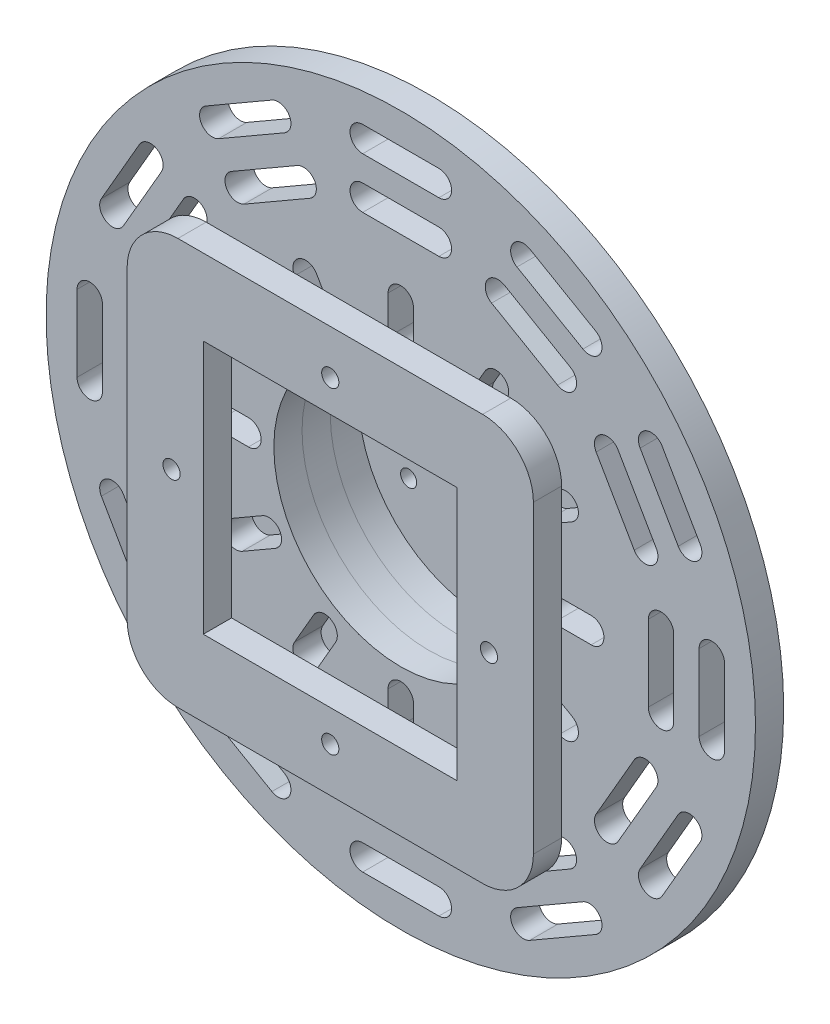
SolidWorks part; units mm, degrees
ref_plane "Front Plane" through (0, 0, 0) normal (0, 0, 1) x (1, 0, 0)
ref_plane "Top Plane" through (0, 0, 0) normal (0, 1, 0) x (1, 0, 0)
ref_plane "Right Plane" through (0, 0, 0) normal (1, 0, 0) x (0, 0, -1)
sketch "Sketch1" plane through (0, 0, 0) normal (0, 0, 1) x (1, 0, 0)
  line L0 (0, -75) -> (0, -60) construction
  line L1 (-5, -75) -> (-5, -60)
  line L2 (5, -75) -> (5, -60)
  line L3 (0, -60) -> (0, 0) construction
  line L4 (-15, -122.5) -> (15, -122.5) construction
  line L7 (-15, -117.5) -> (15, -117.5)
  line L10 (-15, -127.5) -> (15, -127.5)
  line L13 (0, -102.5) -> (0, -122.5) construction
  line L16 (-37.5, -64.9519) -> (-30, -51.9615) construction
  line L19 (-41.8301, -62.4519) -> (-34.3301, -49.4615)
  line L22 (-33.1699, -67.4519) -> (-25.6699, -54.4615)
  line L25 (-64.2404, -81.2676) -> (-38.2596, -96.2676) construction
  line L28 (-61.7404, -76.9375) -> (-35.7596, -91.9375)
  line L31 (-15, -102.5) -> (15, -102.5) construction
  line L32 (-15, -97.5) -> (15, -97.5)
  line L33 (-15, -107.5) -> (15, -107.5)
  line L34 (0, -67.5) -> (0, -102.5) construction
  line L35 (-66.7404, -85.5977) -> (-40.7596, -100.5977)
  line L38 (-74.2404, -98.5881) -> (-48.2596, -113.5881) construction
  line L41 (-71.7404, -94.258) -> (-45.7596, -109.258)
  line L44 (-76.7404, -102.9182) -> (-50.7596, -117.9182)
  line L47 (-64.9519, -37.5) -> (-51.9615, -30) construction
  line L50 (-67.4519, -33.1699) -> (-54.4615, -25.6699)
  line L53 (-62.4519, -41.8301) -> (-49.4615, -34.3301)
  line L56 (-96.2676, -38.2596) -> (-81.2676, -64.2404) construction
  line L59 (-91.9375, -35.7596) -> (-76.9375, -61.7404)
  line L62 (-100.5977, -40.7596) -> (-85.5977, -66.7404)
  line L63 (-113.5881, -48.2596) -> (-98.5881, -74.2404) construction
  line L64 (-109.258, -45.7596) -> (-94.258, -71.7404)
  line L65 (-117.9182, -50.7596) -> (-102.9182, -76.7404)
  line L66 (-75, 0) -> (-60, 0) construction
  line L67 (-75, 5) -> (-60, 5)
  line L68 (-75, -5) -> (-60, -5)
  line L69 (-102.5, 15) -> (-102.5, -15) construction
  line L70 (-97.5, 15) -> (-97.5, -15)
  line L71 (-107.5, 15) -> (-107.5, -15)
  line L72 (-122.5, 15) -> (-122.5, -15) construction
  line L73 (-117.5, 15) -> (-117.5, -15)
  line L74 (-127.5, 15) -> (-127.5, -15)
  line L75 (-64.9519, 37.5) -> (-51.9615, 30) construction
  line L76 (-62.4519, 41.8301) -> (-49.4615, 34.3301)
  line L77 (-67.4519, 33.1699) -> (-54.4615, 25.6699)
  line L78 (-81.2676, 64.2404) -> (-96.2676, 38.2596) construction
  line L79 (-76.9375, 61.7404) -> (-91.9375, 35.7596)
  line L80 (-85.5977, 66.7404) -> (-100.5977, 40.7596)
  line L81 (-98.5881, 74.2404) -> (-113.5881, 48.2596) construction
  line L82 (-94.258, 71.7404) -> (-109.258, 45.7596)
  line L83 (-102.9182, 76.7404) -> (-117.9182, 50.7596)
  line L84 (-37.5, 64.9519) -> (-30, 51.9615) construction
  line L85 (-33.1699, 67.4519) -> (-25.6699, 54.4615)
  line L86 (-41.8301, 62.4519) -> (-34.3301, 49.4615)
  line L87 (-38.2596, 96.2676) -> (-64.2404, 81.2676) construction
  line L88 (-35.7596, 91.9375) -> (-61.7404, 76.9375)
  line L89 (-40.7596, 100.5977) -> (-66.7404, 85.5977)
  line L90 (-48.2596, 113.5881) -> (-74.2404, 98.5881) construction
  line L91 (-45.7596, 109.258) -> (-71.7404, 94.258)
  line L92 (-50.7596, 117.9182) -> (-76.7404, 102.9182)
  line L93 (0, 75) -> (0, 60) construction
  line L94 (5, 75) -> (5, 60)
  line L95 (-5, 75) -> (-5, 60)
  line L96 (15, 102.5) -> (-15, 102.5) construction
  line L97 (15, 97.5) -> (-15, 97.5)
  line L98 (15, 107.5) -> (-15, 107.5)
  line L99 (15, 122.5) -> (-15, 122.5) construction
  line L100 (15, 117.5) -> (-15, 117.5)
  line L101 (15, 127.5) -> (-15, 127.5)
  line L102 (37.5, 64.9519) -> (30, 51.9615) construction
  line L103 (41.8301, 62.4519) -> (34.3301, 49.4615)
  line L104 (33.1699, 67.4519) -> (25.6699, 54.4615)
  line L105 (64.2404, 81.2676) -> (38.2596, 96.2676) construction
  line L106 (61.7404, 76.9375) -> (35.7596, 91.9375)
  line L107 (66.7404, 85.5977) -> (40.7596, 100.5977)
  line L108 (74.2404, 98.5881) -> (48.2596, 113.5881) construction
  line L109 (71.7404, 94.258) -> (45.7596, 109.258)
  line L110 (76.7404, 102.9182) -> (50.7596, 117.9182)
  line L111 (64.9519, 37.5) -> (51.9615, 30) construction
  line L112 (67.4519, 33.1699) -> (54.4615, 25.6699)
  line L113 (62.4519, 41.8301) -> (49.4615, 34.3301)
  line L114 (96.2676, 38.2596) -> (81.2676, 64.2404) construction
  line L115 (91.9375, 35.7596) -> (76.9375, 61.7404)
  line L116 (100.5977, 40.7596) -> (85.5977, 66.7404)
  line L117 (113.5881, 48.2596) -> (98.5881, 74.2404) construction
  line L118 (109.258, 45.7596) -> (94.258, 71.7404)
  line L119 (117.9182, 50.7596) -> (102.9182, 76.7404)
  line L120 (75, 0) -> (60, 0) construction
  line L121 (75, -5) -> (60, -5)
  line L122 (75, 5) -> (60, 5)
  line L123 (102.5, -15) -> (102.5, 15) construction
  line L124 (97.5, -15) -> (97.5, 15)
  line L125 (107.5, -15) -> (107.5, 15)
  line L126 (122.5, -15) -> (122.5, 15) construction
  line L127 (117.5, -15) -> (117.5, 15)
  line L128 (127.5, -15) -> (127.5, 15)
  line L129 (64.9519, -37.5) -> (51.9615, -30) construction
  line L130 (62.4519, -41.8301) -> (49.4615, -34.3301)
  line L131 (67.4519, -33.1699) -> (54.4615, -25.6699)
  line L132 (81.2676, -64.2404) -> (96.2676, -38.2596) construction
  line L133 (76.9375, -61.7404) -> (91.9375, -35.7596)
  line L134 (85.5977, -66.7404) -> (100.5977, -40.7596)
  line L135 (98.5881, -74.2404) -> (113.5881, -48.2596) construction
  line L136 (94.258, -71.7404) -> (109.258, -45.7596)
  line L137 (102.9182, -76.7404) -> (117.9182, -50.7596)
  line L138 (37.5, -64.9519) -> (30, -51.9615) construction
  line L139 (33.1699, -67.4519) -> (25.6699, -54.4615)
  line L140 (41.8301, -62.4519) -> (34.3301, -49.4615)
  line L141 (38.2596, -96.2676) -> (64.2404, -81.2676) construction
  line L142 (35.7596, -91.9375) -> (61.7404, -76.9375)
  line L143 (40.7596, -100.5977) -> (66.7404, -85.5977)
  line L144 (48.2596, -113.5881) -> (74.2404, -98.5881) construction
  line L145 (45.7596, -109.258) -> (71.7404, -94.258)
  line L146 (50.7596, -117.9182) -> (76.7404, -102.9182)
  circle A0 centre (0, 0) radius 139.7
  circle A1 centre (0, 0) radius 25
  arc A2 (-5, -75) -> (5, -75) centre (0, -75) ccw
  arc A3 (5, -60) -> (-5, -60) centre (0, -60) ccw
  arc A22 (-15, -97.5) -> (-15, -107.5) centre (-15, -102.5) ccw
  arc A23 (15, -107.5) -> (15, -97.5) centre (15, -102.5) ccw
  arc A42 (-15, -117.5) -> (-15, -127.5) centre (-15, -122.5) ccw
  arc A43 (15, -127.5) -> (15, -117.5) centre (15, -122.5) ccw
  arc A44 (-41.8301, -62.4519) -> (-33.1699, -67.4519) centre (-37.5, -64.9519) ccw
  arc A45 (-25.6699, -54.4615) -> (-34.3301, -49.4615) centre (-30, -51.9615) ccw
  arc A46 (-61.7404, -76.9375) -> (-66.7404, -85.5977) centre (-64.2404, -81.2676) ccw
  arc A47 (-40.7596, -100.5977) -> (-35.7596, -91.9375) centre (-38.2596, -96.2676) ccw
  arc A48 (-71.7404, -94.258) -> (-76.7404, -102.9182) centre (-74.2404, -98.5881) ccw
  arc A49 (-50.7596, -117.9182) -> (-45.7596, -109.258) centre (-48.2596, -113.5881) ccw
  arc A50 (-67.4519, -33.1699) -> (-62.4519, -41.8301) centre (-64.9519, -37.5) ccw
  arc A51 (-49.4615, -34.3301) -> (-54.4615, -25.6699) centre (-51.9615, -30) ccw
  arc A52 (-91.9375, -35.7596) -> (-100.5977, -40.7596) centre (-96.2676, -38.2596) ccw
  arc A53 (-85.5977, -66.7404) -> (-76.9375, -61.7404) centre (-81.2676, -64.2404) ccw
  arc A54 (-109.258, -45.7596) -> (-117.9182, -50.7596) centre (-113.5881, -48.2596) ccw
  arc A55 (-102.9182, -76.7404) -> (-94.258, -71.7404) centre (-98.5881, -74.2404) ccw
  arc A56 (-75, 5) -> (-75, -5) centre (-75, 0) ccw
  arc A57 (-60, -5) -> (-60, 5) centre (-60, 0) ccw
  arc A58 (-97.5, 15) -> (-107.5, 15) centre (-102.5, 15) ccw
  arc A59 (-107.5, -15) -> (-97.5, -15) centre (-102.5, -15) ccw
  arc A60 (-117.5, 15) -> (-127.5, 15) centre (-122.5, 15) ccw
  arc A61 (-127.5, -15) -> (-117.5, -15) centre (-122.5, -15) ccw
  arc A62 (-62.4519, 41.8301) -> (-67.4519, 33.1699) centre (-64.9519, 37.5) ccw
  arc A63 (-54.4615, 25.6699) -> (-49.4615, 34.3301) centre (-51.9615, 30) ccw
  arc A64 (-76.9375, 61.7404) -> (-85.5977, 66.7404) centre (-81.2676, 64.2404) ccw
  arc A65 (-100.5977, 40.7596) -> (-91.9375, 35.7596) centre (-96.2676, 38.2596) ccw
  arc A66 (-94.258, 71.7404) -> (-102.9182, 76.7404) centre (-98.5881, 74.2404) ccw
  arc A67 (-117.9182, 50.7596) -> (-109.258, 45.7596) centre (-113.5881, 48.2596) ccw
  arc A68 (-33.1699, 67.4519) -> (-41.8301, 62.4519) centre (-37.5, 64.9519) ccw
  arc A69 (-34.3301, 49.4615) -> (-25.6699, 54.4615) centre (-30, 51.9615) ccw
  arc A70 (-35.7596, 91.9375) -> (-40.7596, 100.5977) centre (-38.2596, 96.2676) ccw
  arc A71 (-66.7404, 85.5977) -> (-61.7404, 76.9375) centre (-64.2404, 81.2676) ccw
  arc A72 (-45.7596, 109.258) -> (-50.7596, 117.9182) centre (-48.2596, 113.5881) ccw
  arc A73 (-76.7404, 102.9182) -> (-71.7404, 94.258) centre (-74.2404, 98.5881) ccw
  arc A74 (5, 75) -> (-5, 75) centre (0, 75) ccw
  arc A75 (-5, 60) -> (5, 60) centre (0, 60) ccw
  arc A76 (15, 97.5) -> (15, 107.5) centre (15, 102.5) ccw
  arc A77 (-15, 107.5) -> (-15, 97.5) centre (-15, 102.5) ccw
  arc A78 (15, 117.5) -> (15, 127.5) centre (15, 122.5) ccw
  arc A79 (-15, 127.5) -> (-15, 117.5) centre (-15, 122.5) ccw
  arc A80 (41.8301, 62.4519) -> (33.1699, 67.4519) centre (37.5, 64.9519) ccw
  arc A81 (25.6699, 54.4615) -> (34.3301, 49.4615) centre (30, 51.9615) ccw
  arc A82 (61.7404, 76.9375) -> (66.7404, 85.5977) centre (64.2404, 81.2676) ccw
  arc A83 (40.7596, 100.5977) -> (35.7596, 91.9375) centre (38.2596, 96.2676) ccw
  arc A84 (71.7404, 94.258) -> (76.7404, 102.9182) centre (74.2404, 98.5881) ccw
  arc A85 (50.7596, 117.9182) -> (45.7596, 109.258) centre (48.2596, 113.5881) ccw
  arc A86 (67.4519, 33.1699) -> (62.4519, 41.8301) centre (64.9519, 37.5) ccw
  arc A87 (49.4615, 34.3301) -> (54.4615, 25.6699) centre (51.9615, 30) ccw
  arc A88 (91.9375, 35.7596) -> (100.5977, 40.7596) centre (96.2676, 38.2596) ccw
  arc A89 (85.5977, 66.7404) -> (76.9375, 61.7404) centre (81.2676, 64.2404) ccw
  arc A90 (109.258, 45.7596) -> (117.9182, 50.7596) centre (113.5881, 48.2596) ccw
  arc A91 (102.9182, 76.7404) -> (94.258, 71.7404) centre (98.5881, 74.2404) ccw
  arc A92 (75, -5) -> (75, 5) centre (75, 0) ccw
  arc A93 (60, 5) -> (60, -5) centre (60, 0) ccw
  arc A94 (97.5, -15) -> (107.5, -15) centre (102.5, -15) ccw
  arc A95 (107.5, 15) -> (97.5, 15) centre (102.5, 15) ccw
  arc A96 (117.5, -15) -> (127.5, -15) centre (122.5, -15) ccw
  arc A97 (127.5, 15) -> (117.5, 15) centre (122.5, 15) ccw
  arc A98 (62.4519, -41.8301) -> (67.4519, -33.1699) centre (64.9519, -37.5) ccw
  arc A99 (54.4615, -25.6699) -> (49.4615, -34.3301) centre (51.9615, -30) ccw
  arc A100 (76.9375, -61.7404) -> (85.5977, -66.7404) centre (81.2676, -64.2404) ccw
  arc A101 (100.5977, -40.7596) -> (91.9375, -35.7596) centre (96.2676, -38.2596) ccw
  arc A102 (94.258, -71.7404) -> (102.9182, -76.7404) centre (98.5881, -74.2404) ccw
  arc A103 (117.9182, -50.7596) -> (109.258, -45.7596) centre (113.5881, -48.2596) ccw
  arc A104 (33.1699, -67.4519) -> (41.8301, -62.4519) centre (37.5, -64.9519) ccw
  arc A105 (34.3301, -49.4615) -> (25.6699, -54.4615) centre (30, -51.9615) ccw
  arc A106 (35.7596, -91.9375) -> (40.7596, -100.5977) centre (38.2596, -96.2676) ccw
  arc A107 (66.7404, -85.5977) -> (61.7404, -76.9375) centre (64.2404, -81.2676) ccw
  arc A108 (45.7596, -109.258) -> (50.7596, -117.9182) centre (48.2596, -113.5881) ccw
  arc A109 (76.7404, -102.9182) -> (71.7404, -94.258) centre (74.2404, -98.5881) ccw
  point P6 (0, -67.5)
  point P14 (0, -102.5)
  point P17 (0, -122.5)
  point P29 (-33.75, -58.4567)
  point P36 (-51.25, -88.7676)
  point P39 (-61.25, -106.0881)
  point P51 (-58.4567, -33.75)
  point P60 (-88.7676, -51.25)
  point P63 (-106.0881, -61.25)
  point P75 (-67.5, 0)
  point P78 (-25.429, 35)
  point P89 (-102.5, 0)
  point P93 (-122.5, 0)
  point P105 (-58.4567, 33.75)
  point P113 (-88.7676, 51.25)
  point P116 (-106.0881, 61.25)
  point P127 (-33.75, 58.4567)
  point P135 (-51.25, 88.7676)
  point P138 (-61.25, 106.0881)
  point P151 (0, 67.5)
  point P158 (0, 102.5)
  point P161 (0, 122.5)
  point P172 (33.75, 58.4567)
  point P179 (51.25, 88.7676)
  point P182 (61.25, 106.0881)
  point P193 (58.4567, 33.75)
  point P200 (88.7676, 51.25)
  point P203 (106.0881, 61.25)
  point P214 (67.5, 0)
  point P221 (102.5, 0)
  point P224 (122.5, 0)
  point P235 (58.4567, -33.75)
  point P242 (88.7676, -51.25)
  point P245 (106.0881, -61.25)
  point P256 (33.75, -58.4567)
  point P263 (51.25, -88.7676)
  point P266 (61.25, -106.0881)
  point P275 (0, 0)
  dimension "D1" = 279.4
  dimension "D2" = 50
  dimension "D3" = 60
  dimension "D4" = 15
  dimension "D5" = 10
  dimension "D7" = 30
  dimension "D8" = 10
  dimension "D9" = 35
  dimension "D6" = 20
  dimension "D10" = 12
sketch "Sketch4" plane through (0, 0, 0) normal (0, 0, 1) x (1, 0, 0)
  circle A0 centre (0, 0) radius 12.7
  circle A1 centre (0, 0) radius 75
  circle A2 centre (30.2459, 17.4625) radius 3.175 construction
  circle A3 centre (-30.2459, 17.4625) radius 3.175 construction
  circle A4 centre (0, -34.925) radius 3.175 construction
  circle A5 centre (30.2459, 17.4625) radius 3.175
  circle A6 centre (-30.2459, 17.4625) radius 3.175
  circle A7 centre (0, -34.925) radius 3.175
  arc A8 (-2.2451, 37.1701) -> (0.3966, 38.0751) centre (0, 34.925) ccw construction
  arc A9 (0.3966, 38.0751) -> (-2.2451, 37.1701) centre (0, 34.925) ccw construction
  arc A10 (-2.2451, 37.1701) -> (0.3966, 38.0751) centre (0, 34.925) ccw
  arc A11 (0.3966, 38.0751) -> (-2.2451, 37.1701) centre (0, 34.925) ccw
  arc A12 (-31.0677, -20.5293) -> (-33.1723, -18.6941) centre (-30.2459, -17.4625) ccw construction
  arc A13 (-33.1723, -18.6941) -> (-31.0677, -20.5293) centre (-30.2459, -17.4625) ccw construction
  arc A14 (-31.0677, -20.5293) -> (-33.1723, -18.6941) centre (-30.2459, -17.4625) ccw
  arc A15 (-33.1723, -18.6941) -> (-31.0677, -20.5293) centre (-30.2459, -17.4625) ccw
  arc A16 (33.3128, -16.6407) -> (32.7757, -19.381) centre (30.2459, -17.4625) ccw construction
  arc A17 (32.7757, -19.381) -> (33.3128, -16.6407) centre (30.2459, -17.4625) ccw construction
  arc A18 (33.3128, -16.6407) -> (32.7757, -19.381) centre (30.2459, -17.4625) ccw
  arc A19 (32.7757, -19.381) -> (33.3128, -16.6407) centre (30.2459, -17.4625) ccw
  dimension "D1" = 150
  dimension "D2" = 25.4
extrude "Boss-Extrude1" add sketch "Sketch4" along normal blind 11.1125
sketch "Sketch5" plane through (0, 0, 11.1125) normal (0, 0, 1) x (1, 0, 0)
  circle A0 centre (0, 0) radius 50
  circle A1 centre (0, 0) radius 75
  dimension "D1" = 100
  dimension "D2" = 150
extrude "Boss-Extrude2" add sketch "Sketch5" along normal blind 11.1125 separate body
sketch "Sketch6" plane through (0, 0, 22.225) normal (0, 0, 1) x (1, 0, 0)
  circle A0 centre (0, 0) radius 50
  circle A1 centre (0, 0) radius 90
  dimension "D1" = 180
  dimension "D2" = 100
extrude "Boss-Extrude3" add sketch "Sketch6" along normal blind 11.1125
sketch "Sketch7" plane through (0, 0, 33.3375) normal (0, 0, 1) x (1, 0, 0)
  line L2 (-5, -60) -> (-5, -75)
  line L3 (5, -75) -> (5, -60)
  line L4 (-5, -60) -> (-5, -75)
  line L5 (5, -75) -> (5, -60)
  line L6 (15, -117.5) -> (-15, -117.5)
  line L7 (-15, -127.5) -> (15, -127.5)
  line L8 (15, -117.5) -> (-15, -117.5)
  line L9 (-15, -127.5) -> (15, -127.5)
  line L10 (-45.7596, -109.258) -> (-71.7404, -94.258)
  line L11 (-76.7404, -102.9182) -> (-50.7596, -117.9182)
  line L12 (-45.7596, -109.258) -> (-71.7404, -94.258)
  line L13 (-76.7404, -102.9182) -> (-50.7596, -117.9182)
  line L14 (-33.1699, -67.4519) -> (-25.6699, -54.4615)
  line L15 (-34.3301, -49.4615) -> (-41.8301, -62.4519)
  line L16 (-33.1699, -67.4519) -> (-25.6699, -54.4615)
  line L17 (-34.3301, -49.4615) -> (-41.8301, -62.4519)
  line L18 (-54.4615, -25.6699) -> (-67.4519, -33.1699)
  line L19 (-62.4519, -41.8301) -> (-49.4615, -34.3301)
  line L20 (-54.4615, -25.6699) -> (-67.4519, -33.1699)
  line L21 (-62.4519, -41.8301) -> (-49.4615, -34.3301)
  line L22 (-35.7596, -91.9375) -> (-61.7404, -76.9375)
  line L23 (-66.7404, -85.5977) -> (-40.7596, -100.5977)
  line L24 (-35.7596, -91.9375) -> (-61.7404, -76.9375)
  line L25 (-66.7404, -85.5977) -> (-40.7596, -100.5977)
  line L26 (-94.258, -71.7404) -> (-109.258, -45.7596)
  line L27 (-117.9182, -50.7596) -> (-102.9182, -76.7404)
  line L28 (-94.258, -71.7404) -> (-109.258, -45.7596)
  line L29 (-117.9182, -50.7596) -> (-102.9182, -76.7404)
  line L30 (-76.9375, -61.7404) -> (-91.9375, -35.7596)
  line L31 (-100.5977, -40.7596) -> (-85.5977, -66.7404)
  line L32 (-76.9375, -61.7404) -> (-91.9375, -35.7596)
  line L33 (-100.5977, -40.7596) -> (-85.5977, -66.7404)
  line L34 (-75, -5) -> (-60, -5)
  line L35 (-60, 5) -> (-75, 5)
  line L36 (-75, -5) -> (-60, -5)
  line L37 (-60, 5) -> (-75, 5)
  line L38 (-15, -107.5) -> (15, -107.5)
  line L39 (15, -97.5) -> (-15, -97.5)
  line L40 (-15, -107.5) -> (15, -107.5)
  line L41 (15, -97.5) -> (-15, -97.5)
  line L42 (-49.4615, 34.3301) -> (-62.4519, 41.8301)
  line L43 (-67.4519, 33.1699) -> (-54.4615, 25.6699)
  line L44 (-49.4615, 34.3301) -> (-62.4519, 41.8301)
  line L45 (-67.4519, 33.1699) -> (-54.4615, 25.6699)
  line L46 (-127.5, 15) -> (-127.5, -15)
  line L47 (-117.5, -15) -> (-117.5, 15)
  line L48 (-127.5, 15) -> (-127.5, -15)
  line L49 (-117.5, -15) -> (-117.5, 15)
  line L50 (-97.5, -15) -> (-97.5, 15)
  line L51 (-107.5, 15) -> (-107.5, -15)
  line L52 (-97.5, -15) -> (-97.5, 15)
  line L53 (-107.5, 15) -> (-107.5, -15)
  line L54 (-109.258, 45.7596) -> (-94.258, 71.7404)
  line L55 (-102.9182, 76.7404) -> (-117.9182, 50.7596)
  line L56 (-109.258, 45.7596) -> (-94.258, 71.7404)
  line L57 (-102.9182, 76.7404) -> (-117.9182, 50.7596)
  line L58 (-91.9375, 35.7596) -> (-76.9375, 61.7404)
  line L59 (-85.5977, 66.7404) -> (-100.5977, 40.7596)
  line L60 (-91.9375, 35.7596) -> (-76.9375, 61.7404)
  line L61 (-85.5977, 66.7404) -> (-100.5977, 40.7596)
  line L62 (-71.7404, 94.258) -> (-45.7596, 109.258)
  line L63 (-50.7596, 117.9182) -> (-76.7404, 102.9182)
  line L64 (-71.7404, 94.258) -> (-45.7596, 109.258)
  line L65 (-50.7596, 117.9182) -> (-76.7404, 102.9182)
  line L66 (-25.6699, 54.4615) -> (-33.1699, 67.4519)
  line L67 (-41.8301, 62.4519) -> (-34.3301, 49.4615)
  line L68 (-25.6699, 54.4615) -> (-33.1699, 67.4519)
  line L69 (-41.8301, 62.4519) -> (-34.3301, 49.4615)
  line L70 (5, 60) -> (5, 75)
  line L71 (-5, 75) -> (-5, 60)
  line L72 (5, 60) -> (5, 75)
  line L73 (-5, 75) -> (-5, 60)
  line L74 (-61.7404, 76.9375) -> (-35.7596, 91.9375)
  line L75 (-40.7596, 100.5977) -> (-66.7404, 85.5977)
  line L76 (-61.7404, 76.9375) -> (-35.7596, 91.9375)
  line L77 (-40.7596, 100.5977) -> (-66.7404, 85.5977)
  line L78 (-15, 117.5) -> (15, 117.5)
  line L79 (15, 127.5) -> (-15, 127.5)
  line L80 (-15, 117.5) -> (15, 117.5)
  line L81 (15, 127.5) -> (-15, 127.5)
  line L82 (-15, 97.5) -> (15, 97.5)
  line L83 (15, 107.5) -> (-15, 107.5)
  line L84 (-15, 97.5) -> (15, 97.5)
  line L85 (15, 107.5) -> (-15, 107.5)
  line L86 (45.7596, 109.258) -> (71.7404, 94.258)
  line L87 (76.7404, 102.9182) -> (50.7596, 117.9182)
  line L88 (45.7596, 109.258) -> (71.7404, 94.258)
  line L89 (76.7404, 102.9182) -> (50.7596, 117.9182)
  line L90 (35.7596, 91.9375) -> (61.7404, 76.9375)
  line L91 (66.7404, 85.5977) -> (40.7596, 100.5977)
  line L92 (35.7596, 91.9375) -> (61.7404, 76.9375)
  line L93 (66.7404, 85.5977) -> (40.7596, 100.5977)
  line L94 (34.3301, 49.4615) -> (41.8301, 62.4519)
  line L95 (33.1699, 67.4519) -> (25.6699, 54.4615)
  line L96 (34.3301, 49.4615) -> (41.8301, 62.4519)
  line L97 (33.1699, 67.4519) -> (25.6699, 54.4615)
  line L98 (94.258, 71.7404) -> (109.258, 45.7596)
  line L99 (117.9182, 50.7596) -> (102.9182, 76.7404)
  line L100 (94.258, 71.7404) -> (109.258, 45.7596)
  line L101 (117.9182, 50.7596) -> (102.9182, 76.7404)
  line L102 (54.4615, 25.6699) -> (67.4519, 33.1699)
  line L103 (62.4519, 41.8301) -> (49.4615, 34.3301)
  line L104 (54.4615, 25.6699) -> (67.4519, 33.1699)
  line L105 (62.4519, 41.8301) -> (49.4615, 34.3301)
  line L106 (60, -5) -> (75, -5)
  line L107 (75, 5) -> (60, 5)
  line L108 (60, -5) -> (75, -5)
  line L109 (75, 5) -> (60, 5)
  line L110 (76.9375, 61.7404) -> (91.9375, 35.7596)
  line L111 (100.5977, 40.7596) -> (85.5977, 66.7404)
  line L112 (76.9375, 61.7404) -> (91.9375, 35.7596)
  line L113 (100.5977, 40.7596) -> (85.5977, 66.7404)
  line L114 (49.4615, -34.3301) -> (62.4519, -41.8301)
  line L115 (67.4519, -33.1699) -> (54.4615, -25.6699)
  line L116 (49.4615, -34.3301) -> (62.4519, -41.8301)
  line L117 (67.4519, -33.1699) -> (54.4615, -25.6699)
  line L118 (117.5, 15) -> (117.5, -15)
  line L119 (127.5, -15) -> (127.5, 15)
  line L120 (117.5, 15) -> (117.5, -15)
  line L121 (127.5, -15) -> (127.5, 15)
  line L122 (97.5, 15) -> (97.5, -15)
  line L123 (107.5, -15) -> (107.5, 15)
  line L124 (97.5, 15) -> (97.5, -15)
  line L125 (107.5, -15) -> (107.5, 15)
  line L126 (109.258, -45.7596) -> (94.258, -71.7404)
  line L127 (102.9182, -76.7404) -> (117.9182, -50.7596)
  line L128 (109.258, -45.7596) -> (94.258, -71.7404)
  line L129 (102.9182, -76.7404) -> (117.9182, -50.7596)
  line L130 (91.9375, -35.7596) -> (76.9375, -61.7404)
  line L131 (85.5977, -66.7404) -> (100.5977, -40.7596)
  line L132 (91.9375, -35.7596) -> (76.9375, -61.7404)
  line L133 (85.5977, -66.7404) -> (100.5977, -40.7596)
  line L134 (71.7404, -94.258) -> (45.7596, -109.258)
  line L135 (50.7596, -117.9182) -> (76.7404, -102.9182)
  line L136 (71.7404, -94.258) -> (45.7596, -109.258)
  line L137 (50.7596, -117.9182) -> (76.7404, -102.9182)
  line L138 (61.7404, -76.9375) -> (35.7596, -91.9375)
  line L139 (40.7596, -100.5977) -> (66.7404, -85.5977)
  line L140 (61.7404, -76.9375) -> (35.7596, -91.9375)
  line L141 (40.7596, -100.5977) -> (66.7404, -85.5977)
  line L142 (25.6699, -54.4615) -> (33.1699, -67.4519)
  line L143 (41.8301, -62.4519) -> (34.3301, -49.4615)
  line L144 (25.6699, -54.4615) -> (33.1699, -67.4519)
  line L145 (41.8301, -62.4519) -> (34.3301, -49.4615)
  circle A0 centre (0, 0) radius 50
  circle A3 centre (0, 0) radius 139.7
  circle A4 centre (0, 0) radius 139.7
  arc A6 (5, -60) -> (-5, -60) centre (0, -60) ccw
  arc A7 (-5, -75) -> (5, -75) centre (0, -75) ccw
  arc A8 (5, -60) -> (-5, -60) centre (0, -60) ccw
  arc A9 (-5, -75) -> (5, -75) centre (0, -75) ccw
  arc A10 (15, -127.5) -> (15, -117.5) centre (15, -122.5) ccw
  arc A11 (-15, -117.5) -> (-15, -127.5) centre (-15, -122.5) ccw
  arc A12 (15, -127.5) -> (15, -117.5) centre (15, -122.5) ccw
  arc A13 (-15, -117.5) -> (-15, -127.5) centre (-15, -122.5) ccw
  arc A14 (-50.7596, -117.9182) -> (-45.7596, -109.258) centre (-48.2596, -113.5881) ccw
  arc A15 (-71.7404, -94.258) -> (-76.7404, -102.9182) centre (-74.2404, -98.5881) ccw
  arc A16 (-50.7596, -117.9182) -> (-45.7596, -109.258) centre (-48.2596, -113.5881) ccw
  arc A17 (-71.7404, -94.258) -> (-76.7404, -102.9182) centre (-74.2404, -98.5881) ccw
  arc A18 (-25.6699, -54.4615) -> (-34.3301, -49.4615) centre (-30, -51.9615) ccw
  arc A19 (-41.8301, -62.4519) -> (-33.1699, -67.4519) centre (-37.5, -64.9519) ccw
  arc A20 (-25.6699, -54.4615) -> (-34.3301, -49.4615) centre (-30, -51.9615) ccw
  arc A21 (-41.8301, -62.4519) -> (-33.1699, -67.4519) centre (-37.5, -64.9519) ccw
  arc A22 (-49.4615, -34.3301) -> (-54.4615, -25.6699) centre (-51.9615, -30) ccw
  arc A23 (-67.4519, -33.1699) -> (-62.4519, -41.8301) centre (-64.9519, -37.5) ccw
  arc A24 (-49.4615, -34.3301) -> (-54.4615, -25.6699) centre (-51.9615, -30) ccw
  arc A25 (-67.4519, -33.1699) -> (-62.4519, -41.8301) centre (-64.9519, -37.5) ccw
  arc A26 (-40.7596, -100.5977) -> (-35.7596, -91.9375) centre (-38.2596, -96.2676) ccw
  arc A27 (-61.7404, -76.9375) -> (-66.7404, -85.5977) centre (-64.2404, -81.2676) ccw
  arc A28 (-40.7596, -100.5977) -> (-35.7596, -91.9375) centre (-38.2596, -96.2676) ccw
  arc A29 (-61.7404, -76.9375) -> (-66.7404, -85.5977) centre (-64.2404, -81.2676) ccw
  arc A30 (-102.9182, -76.7404) -> (-94.258, -71.7404) centre (-98.5881, -74.2404) ccw
  arc A31 (-109.258, -45.7596) -> (-117.9182, -50.7596) centre (-113.5881, -48.2596) ccw
  arc A32 (-102.9182, -76.7404) -> (-94.258, -71.7404) centre (-98.5881, -74.2404) ccw
  arc A33 (-109.258, -45.7596) -> (-117.9182, -50.7596) centre (-113.5881, -48.2596) ccw
  arc A34 (-85.5977, -66.7404) -> (-76.9375, -61.7404) centre (-81.2676, -64.2404) ccw
  arc A35 (-91.9375, -35.7596) -> (-100.5977, -40.7596) centre (-96.2676, -38.2596) ccw
  arc A36 (-85.5977, -66.7404) -> (-76.9375, -61.7404) centre (-81.2676, -64.2404) ccw
  arc A37 (-91.9375, -35.7596) -> (-100.5977, -40.7596) centre (-96.2676, -38.2596) ccw
  arc A38 (-60, -5) -> (-60, 5) centre (-60, 0) ccw
  arc A39 (-75, 5) -> (-75, -5) centre (-75, 0) ccw
  arc A40 (-60, -5) -> (-60, 5) centre (-60, 0) ccw
  arc A41 (-75, 5) -> (-75, -5) centre (-75, 0) ccw
  arc A42 (15, -107.5) -> (15, -97.5) centre (15, -102.5) ccw
  arc A43 (-15, -97.5) -> (-15, -107.5) centre (-15, -102.5) ccw
  arc A44 (15, -107.5) -> (15, -97.5) centre (15, -102.5) ccw
  arc A45 (-15, -97.5) -> (-15, -107.5) centre (-15, -102.5) ccw
  arc A46 (-54.4615, 25.6699) -> (-49.4615, 34.3301) centre (-51.9615, 30) ccw
  arc A47 (-62.4519, 41.8301) -> (-67.4519, 33.1699) centre (-64.9519, 37.5) ccw
  arc A48 (-54.4615, 25.6699) -> (-49.4615, 34.3301) centre (-51.9615, 30) ccw
  arc A49 (-62.4519, 41.8301) -> (-67.4519, 33.1699) centre (-64.9519, 37.5) ccw
  arc A50 (-127.5, -15) -> (-117.5, -15) centre (-122.5, -15) ccw
  arc A51 (-117.5, 15) -> (-127.5, 15) centre (-122.5, 15) ccw
  arc A52 (-127.5, -15) -> (-117.5, -15) centre (-122.5, -15) ccw
  arc A53 (-117.5, 15) -> (-127.5, 15) centre (-122.5, 15) ccw
  arc A54 (-107.5, -15) -> (-97.5, -15) centre (-102.5, -15) ccw
  arc A55 (-97.5, 15) -> (-107.5, 15) centre (-102.5, 15) ccw
  arc A56 (-107.5, -15) -> (-97.5, -15) centre (-102.5, -15) ccw
  arc A57 (-97.5, 15) -> (-107.5, 15) centre (-102.5, 15) ccw
  arc A58 (-117.9182, 50.7596) -> (-109.258, 45.7596) centre (-113.5881, 48.2596) ccw
  arc A59 (-94.258, 71.7404) -> (-102.9182, 76.7404) centre (-98.5881, 74.2404) ccw
  arc A60 (-117.9182, 50.7596) -> (-109.258, 45.7596) centre (-113.5881, 48.2596) ccw
  arc A61 (-94.258, 71.7404) -> (-102.9182, 76.7404) centre (-98.5881, 74.2404) ccw
  arc A62 (-100.5977, 40.7596) -> (-91.9375, 35.7596) centre (-96.2676, 38.2596) ccw
  arc A63 (-76.9375, 61.7404) -> (-85.5977, 66.7404) centre (-81.2676, 64.2404) ccw
  arc A64 (-100.5977, 40.7596) -> (-91.9375, 35.7596) centre (-96.2676, 38.2596) ccw
  arc A65 (-76.9375, 61.7404) -> (-85.5977, 66.7404) centre (-81.2676, 64.2404) ccw
  arc A66 (-76.7404, 102.9182) -> (-71.7404, 94.258) centre (-74.2404, 98.5881) ccw
  arc A67 (-45.7596, 109.258) -> (-50.7596, 117.9182) centre (-48.2596, 113.5881) ccw
  arc A68 (-76.7404, 102.9182) -> (-71.7404, 94.258) centre (-74.2404, 98.5881) ccw
  arc A69 (-45.7596, 109.258) -> (-50.7596, 117.9182) centre (-48.2596, 113.5881) ccw
  arc A70 (-34.3301, 49.4615) -> (-25.6699, 54.4615) centre (-30, 51.9615) ccw
  arc A71 (-33.1699, 67.4519) -> (-41.8301, 62.4519) centre (-37.5, 64.9519) ccw
  arc A72 (-34.3301, 49.4615) -> (-25.6699, 54.4615) centre (-30, 51.9615) ccw
  arc A73 (-33.1699, 67.4519) -> (-41.8301, 62.4519) centre (-37.5, 64.9519) ccw
  arc A74 (-5, 60) -> (5, 60) centre (0, 60) ccw
  arc A75 (5, 75) -> (-5, 75) centre (0, 75) ccw
  arc A76 (-5, 60) -> (5, 60) centre (0, 60) ccw
  arc A77 (5, 75) -> (-5, 75) centre (0, 75) ccw
  arc A78 (-66.7404, 85.5977) -> (-61.7404, 76.9375) centre (-64.2404, 81.2676) ccw
  arc A79 (-35.7596, 91.9375) -> (-40.7596, 100.5977) centre (-38.2596, 96.2676) ccw
  arc A80 (-66.7404, 85.5977) -> (-61.7404, 76.9375) centre (-64.2404, 81.2676) ccw
  arc A81 (-35.7596, 91.9375) -> (-40.7596, 100.5977) centre (-38.2596, 96.2676) ccw
  arc A82 (-15, 127.5) -> (-15, 117.5) centre (-15, 122.5) ccw
  arc A83 (15, 117.5) -> (15, 127.5) centre (15, 122.5) ccw
  arc A84 (-15, 127.5) -> (-15, 117.5) centre (-15, 122.5) ccw
  arc A85 (15, 117.5) -> (15, 127.5) centre (15, 122.5) ccw
  arc A86 (-15, 107.5) -> (-15, 97.5) centre (-15, 102.5) ccw
  arc A87 (15, 97.5) -> (15, 107.5) centre (15, 102.5) ccw
  arc A88 (-15, 107.5) -> (-15, 97.5) centre (-15, 102.5) ccw
  arc A89 (15, 97.5) -> (15, 107.5) centre (15, 102.5) ccw
  arc A90 (50.7596, 117.9182) -> (45.7596, 109.258) centre (48.2596, 113.5881) ccw
  arc A91 (71.7404, 94.258) -> (76.7404, 102.9182) centre (74.2404, 98.5881) ccw
  arc A92 (50.7596, 117.9182) -> (45.7596, 109.258) centre (48.2596, 113.5881) ccw
  arc A93 (71.7404, 94.258) -> (76.7404, 102.9182) centre (74.2404, 98.5881) ccw
  arc A94 (40.7596, 100.5977) -> (35.7596, 91.9375) centre (38.2596, 96.2676) ccw
  arc A95 (61.7404, 76.9375) -> (66.7404, 85.5977) centre (64.2404, 81.2676) ccw
  arc A96 (40.7596, 100.5977) -> (35.7596, 91.9375) centre (38.2596, 96.2676) ccw
  arc A97 (61.7404, 76.9375) -> (66.7404, 85.5977) centre (64.2404, 81.2676) ccw
  arc A98 (25.6699, 54.4615) -> (34.3301, 49.4615) centre (30, 51.9615) ccw
  arc A99 (41.8301, 62.4519) -> (33.1699, 67.4519) centre (37.5, 64.9519) ccw
  arc A100 (25.6699, 54.4615) -> (34.3301, 49.4615) centre (30, 51.9615) ccw
  arc A101 (41.8301, 62.4519) -> (33.1699, 67.4519) centre (37.5, 64.9519) ccw
  arc A102 (102.9182, 76.7404) -> (94.258, 71.7404) centre (98.5881, 74.2404) ccw
  arc A103 (109.258, 45.7596) -> (117.9182, 50.7596) centre (113.5881, 48.2596) ccw
  arc A104 (102.9182, 76.7404) -> (94.258, 71.7404) centre (98.5881, 74.2404) ccw
  arc A105 (109.258, 45.7596) -> (117.9182, 50.7596) centre (113.5881, 48.2596) ccw
  arc A106 (49.4615, 34.3301) -> (54.4615, 25.6699) centre (51.9615, 30) ccw
  arc A107 (67.4519, 33.1699) -> (62.4519, 41.8301) centre (64.9519, 37.5) ccw
  arc A108 (49.4615, 34.3301) -> (54.4615, 25.6699) centre (51.9615, 30) ccw
  arc A109 (67.4519, 33.1699) -> (62.4519, 41.8301) centre (64.9519, 37.5) ccw
  arc A110 (60, 5) -> (60, -5) centre (60, 0) ccw
  arc A111 (75, -5) -> (75, 5) centre (75, 0) ccw
  arc A112 (60, 5) -> (60, -5) centre (60, 0) ccw
  arc A113 (75, -5) -> (75, 5) centre (75, 0) ccw
  arc A114 (85.5977, 66.7404) -> (76.9375, 61.7404) centre (81.2676, 64.2404) ccw
  arc A115 (91.9375, 35.7596) -> (100.5977, 40.7596) centre (96.2676, 38.2596) ccw
  arc A116 (85.5977, 66.7404) -> (76.9375, 61.7404) centre (81.2676, 64.2404) ccw
  arc A117 (91.9375, 35.7596) -> (100.5977, 40.7596) centre (96.2676, 38.2596) ccw
  arc A118 (54.4615, -25.6699) -> (49.4615, -34.3301) centre (51.9615, -30) ccw
  arc A119 (62.4519, -41.8301) -> (67.4519, -33.1699) centre (64.9519, -37.5) ccw
  arc A120 (54.4615, -25.6699) -> (49.4615, -34.3301) centre (51.9615, -30) ccw
  arc A121 (62.4519, -41.8301) -> (67.4519, -33.1699) centre (64.9519, -37.5) ccw
  arc A122 (127.5, 15) -> (117.5, 15) centre (122.5, 15) ccw
  arc A123 (117.5, -15) -> (127.5, -15) centre (122.5, -15) ccw
  arc A124 (127.5, 15) -> (117.5, 15) centre (122.5, 15) ccw
  arc A125 (117.5, -15) -> (127.5, -15) centre (122.5, -15) ccw
  arc A126 (107.5, 15) -> (97.5, 15) centre (102.5, 15) ccw
  arc A127 (97.5, -15) -> (107.5, -15) centre (102.5, -15) ccw
  arc A128 (107.5, 15) -> (97.5, 15) centre (102.5, 15) ccw
  arc A129 (97.5, -15) -> (107.5, -15) centre (102.5, -15) ccw
  arc A130 (117.9182, -50.7596) -> (109.258, -45.7596) centre (113.5881, -48.2596) ccw
  arc A131 (94.258, -71.7404) -> (102.9182, -76.7404) centre (98.5881, -74.2404) ccw
  arc A132 (117.9182, -50.7596) -> (109.258, -45.7596) centre (113.5881, -48.2596) ccw
  arc A133 (94.258, -71.7404) -> (102.9182, -76.7404) centre (98.5881, -74.2404) ccw
  arc A134 (100.5977, -40.7596) -> (91.9375, -35.7596) centre (96.2676, -38.2596) ccw
  arc A135 (76.9375, -61.7404) -> (85.5977, -66.7404) centre (81.2676, -64.2404) ccw
  arc A136 (100.5977, -40.7596) -> (91.9375, -35.7596) centre (96.2676, -38.2596) ccw
  arc A137 (76.9375, -61.7404) -> (85.5977, -66.7404) centre (81.2676, -64.2404) ccw
  arc A138 (76.7404, -102.9182) -> (71.7404, -94.258) centre (74.2404, -98.5881) ccw
  arc A139 (45.7596, -109.258) -> (50.7596, -117.9182) centre (48.2596, -113.5881) ccw
  arc A140 (76.7404, -102.9182) -> (71.7404, -94.258) centre (74.2404, -98.5881) ccw
  arc A141 (45.7596, -109.258) -> (50.7596, -117.9182) centre (48.2596, -113.5881) ccw
  arc A142 (66.7404, -85.5977) -> (61.7404, -76.9375) centre (64.2404, -81.2676) ccw
  arc A143 (35.7596, -91.9375) -> (40.7596, -100.5977) centre (38.2596, -96.2676) ccw
  arc A144 (66.7404, -85.5977) -> (61.7404, -76.9375) centre (64.2404, -81.2676) ccw
  arc A145 (35.7596, -91.9375) -> (40.7596, -100.5977) centre (38.2596, -96.2676) ccw
  arc A146 (34.3301, -49.4615) -> (25.6699, -54.4615) centre (30, -51.9615) ccw
  arc A147 (33.1699, -67.4519) -> (41.8301, -62.4519) centre (37.5, -64.9519) ccw
  arc A148 (34.3301, -49.4615) -> (25.6699, -54.4615) centre (30, -51.9615) ccw
  arc A149 (33.1699, -67.4519) -> (41.8301, -62.4519) centre (37.5, -64.9519) ccw
  circle M147 centre (0, 0) radius 90
  dimension "D2" = 0
  dimension "D3" = 0
  dimension "D4" = 0
  dimension "D5" = 0
  dimension "D6" = 0
  dimension "D7" = 0
  dimension "D8" = 0
  dimension "D9" = 0
  dimension "D10" = 0
  dimension "D11" = 0
  dimension "D12" = 0
  dimension "D13" = 0
  dimension "D14" = 0
  dimension "D15" = 0
  dimension "D16" = 0
  dimension "D17" = 0
  dimension "D18" = 0
  dimension "D19" = 0
  dimension "D20" = 0
  dimension "D21" = 0
  dimension "D22" = 0
  dimension "D23" = 0
  dimension "D24" = 0
  dimension "D25" = 0
  dimension "D26" = 0
  dimension "D27" = 0
  dimension "D28" = 0
  dimension "D29" = 0
  dimension "D30" = 0
  dimension "D31" = 0
  dimension "D32" = 0
  dimension "D33" = 0
  dimension "D34" = 0
  dimension "D35" = 0
  dimension "D36" = 0
  dimension "D37" = 0
  dimension "D38" = 0
extrude "Boss-Extrude4" add sketch "Sketch7" along normal blind 11.1125 separate body contours A4 A145 L140 A144 L141 A141 L136 A140 L137 A137 L132 A136 L133 A133 L128 A132 L129 A129 L124 A128 L125 A125 L120 A124 L121 A117 L112 A116 L113 A105 L100 A104 L101 A97 L92 A96 L93 A93 L88 A92 L89 | A149 L144 A148 L145 A121 L116 A120 L117 A113 L108 A112 L109 A109 L104 A108 L105 A101 L96 A100 L97 A77 L72 A76 L73 A73 L68 A72 L69 A49 L44 A48 L45 A41 L37 A40 L36 A25 L20 A24 L21 M147
sketch "Sketch9" plane through (0, 0, 11.1125) normal (0, 0, 1) x (1, 0, 0)
  circle A0 centre (0, 62.5) radius 3.3782
  circle A1 centre (62.5, 0) radius 3.3782
  circle A2 centre (0, -62.5) radius 3.3782
  circle A3 centre (-62.5, 0) radius 3.3782
  circle A4 centre (0, 0) radius 90
  circle A5 centre (0, 0) radius 50
sketch "Sketch8" plane through (0, 0, 11.1125) normal (0, 0, 1) x (1, 0, 0)
  line L0 (-80, 80) -> (80, -80) construction
  line L1 (-60, 80) -> (60, 80)
  line L2 (-80, 60) -> (-80, -60)
  line L3 (-60, -80) -> (60, -80)
  line L4 (80, 60) -> (80, -60)
  line L5 (-50, 50) -> (-50, -50)
  line L6 (-50, -50) -> (50, -50)
  line L7 (50, 50) -> (50, -50)
  line L8 (-50, 50) -> (50, 50)
  line L9 (-80, -80) -> (80, -80) construction
  line L10 (80, 80) -> (80, -80) construction
  line L11 (-80, 80) -> (80, 80) construction
  line L12 (-80, 80) -> (-80, -80) construction
  circle A0 centre (-62.5, 0) radius 3.3782 construction
  circle A1 centre (0, 62.5) radius 3.3782 construction
  circle A2 centre (62.5, 0) radius 3.3782 construction
  circle A3 centre (0, -62.5) radius 3.3782 construction
  circle A4 centre (-62.5, 0) radius 3.3782
  circle A5 centre (0, 62.5) radius 3.3782
  circle A6 centre (62.5, 0) radius 3.3782
  circle A7 centre (0, -62.5) radius 3.3782
  arc A8 (60, -80) -> (80, -60) centre (60, -60) ccw
  arc A9 (-60, 80) -> (-80, 60) centre (-60, 60) ccw
  arc A10 (-80, -60) -> (-60, -80) centre (-60, -60) ccw
  arc A11 (60, 80) -> (80, 60) centre (60, 60) cw
  dimension "D4" = 20
  dimension "D1" = 20
  dimension "D3" = 30
extrude "Boss-Extrude5" add sketch "Sketch8" along normal blind 11.1125 from offset 50 separate body
sketch "Sketch10" plane through (0, 0, 11.1125) normal (0, 0, 1) x (1, 0, 0)
  circle A0 centre (62.5, 0) radius 3.3782 construction
  circle A1 centre (0, 62.5) radius 3.3782 construction
  circle A2 centre (0, -62.5) radius 3.3782 construction
  circle A3 centre (-62.5, 0) radius 3.3782 construction
  circle A4 centre (62.5, 0) radius 3.3782
  circle A5 centre (0, 62.5) radius 3.3782
  circle A6 centre (0, -62.5) radius 3.3782
  circle A7 centre (-62.5, 0) radius 3.3782
extrude "Cut-Extrude1" cut sketch "Sketch10" against normal blind 11.1125
